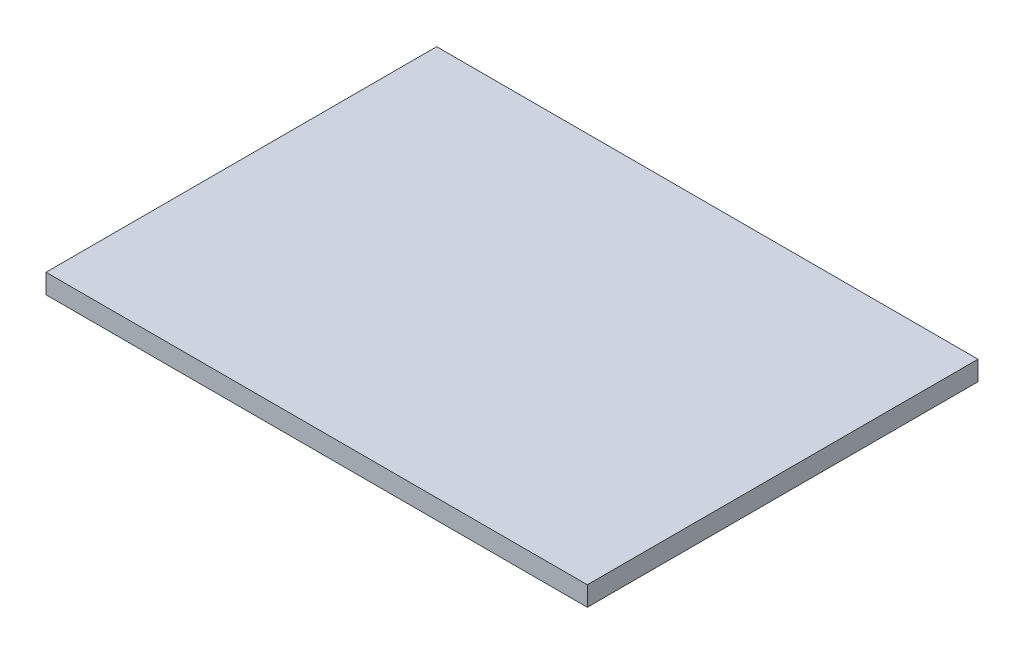
SolidWorks part; units mm, degrees
ref_plane "Front Plane" through (0, 0, 0) normal (0, 0, 1) x (1, 0, 0)
ref_plane "Top Plane" through (0, 0, 0) normal (0, 1, 0) x (1, 0, 0)
ref_plane "Right Plane" through (0, 0, 0) normal (1, 0, 0) x (0, 0, -1)
sketch "Sketch1" plane through (0, 0, 0) normal (0, 1, 0) x (1, 0, 0)
  line L0 (0, 0) -> (-175.9763, 0)
  line L1 (-175.9763, 0) -> (-175.9763, 127)
  line L2 (-175.9763, 127) -> (0, 127)
  line L3 (0, 127) -> (0, 0)
extrude "Boss-Extrude3" add sketch "Sketch1" along normal blind 6.35 contours L3 L0 L1 L2
